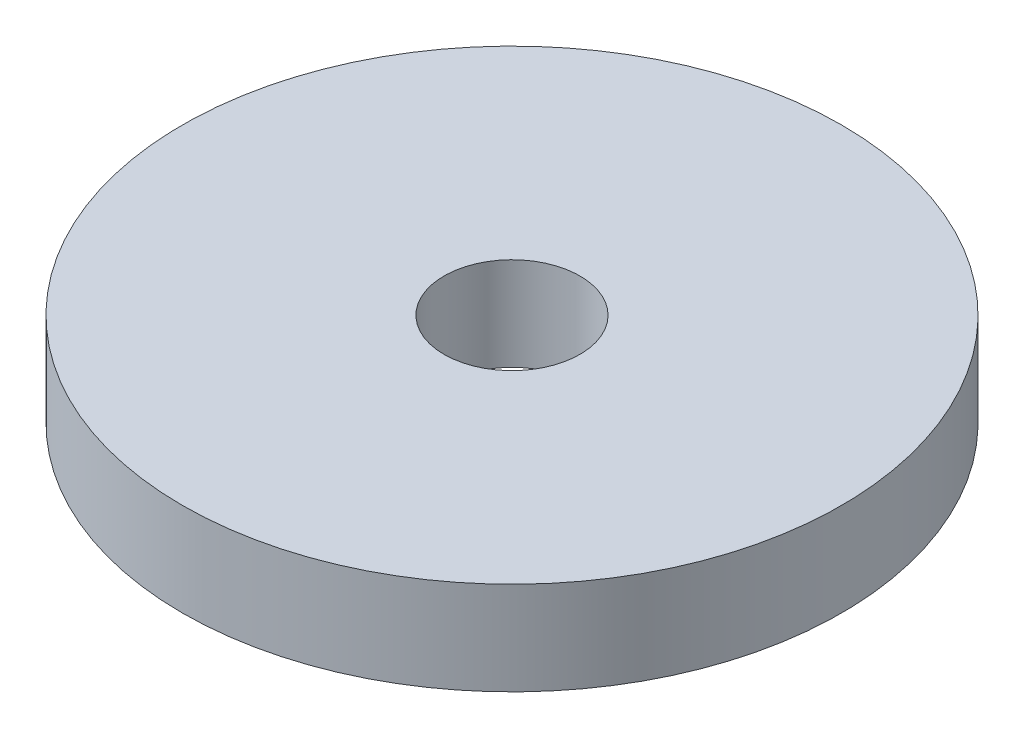
SolidWorks part; units mm, degrees
ref_plane "Front Plane" through (0, 0, 0) normal (0, 0, 1) x (1, 0, 0)
ref_plane "Top Plane" through (0, 0, 0) normal (0, 1, 0) x (1, 0, 0)
ref_plane "Right Plane" through (0, 0, 0) normal (1, 0, 0) x (0, 0, -1)
sketch "Sketch1" plane through (0, 0, 0) normal (0, 1, 0) x (1, 0, 0)
  circle A0 centre (0, 0) radius 24.25
extrude "Boss-Extrude1" add sketch "Sketch1" along normal blind 6.86
sketch "Sketch2" plane through (0, 0, 0) normal (0, 1, 0) x (1, 0, 0)
  circle A0 centre (0, 0) radius 5
extrude "Cut-Extrude2" cut sketch "Sketch2" along normal blind 6.86
